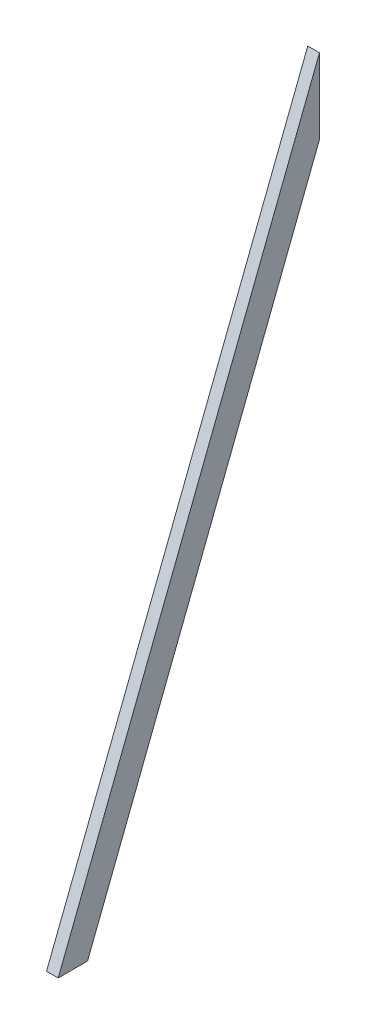
SolidWorks part; units mm, degrees
ref_plane "Front Plane" through (0, 0, 0) normal (0, 0, 1) x (1, 0, 0)
ref_plane "Top Plane" through (0, 0, 0) normal (0, 1, 0) x (1, 0, 0)
ref_plane "Right Plane" through (0, 0, 0) normal (1, 0, 0) x (0, 0, -1)
sketch "Sketch1" plane through (0, 0, 0) normal (1, 0, 0) x (0, 0, -1)
  line L0 (-425.45, -1092.2) -> (-330.0434, -1092.2)
  line L1 (-425.45, -1092.2) -> (425.45, -1092.2) construction
  line L2 (-425.45, -1092.2) -> (-425.45, 1092.2) construction
  line L3 (-425.45, 1092.2) -> (425.45, 1092.2) construction
  line L4 (425.45, -1092.2) -> (425.45, 1092.2) construction
  line L5 (-425.45, -1092.2) -> (425.45, 1092.2)
  line L6 (-425.45, 1092.2) -> (425.45, -1092.2) construction
  line L7 (-330.0434, -1092.2) -> (425.45, 847.2755)
  line L8 (425.45, 847.2755) -> (425.45, 1092.2)
  line L9 (425.45, 847.2755) -> (342.6129, 879.5435) construction
  line L10 (-330.0434, -1092.2) -> (-412.8805, -1059.932) construction
  point P0 (0, 0)
  dimension "D1" = 850.9
  dimension "D2" = 2184.4
  dimension "D3" = 88.9
  dimension "D4" = 228.2209
  dimension "D5" = 68.717
  dimension "D6" = 34.6297
extrude "Boss-Extrude1" add sketch "Sketch1" along normal blind 38.1
